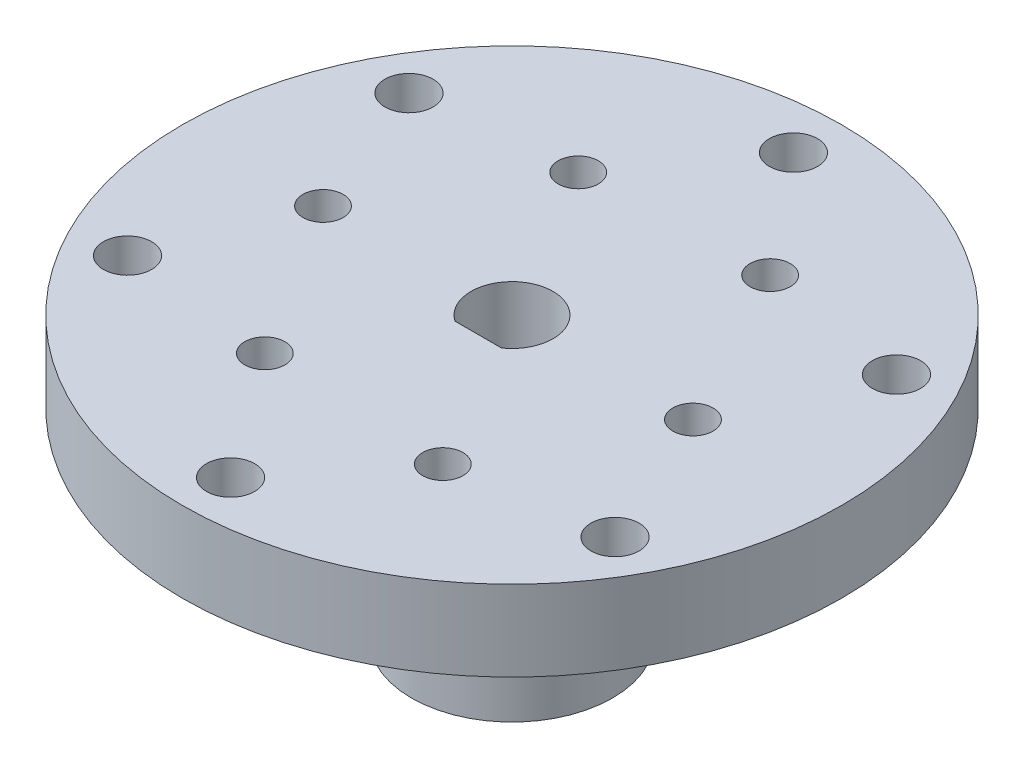
SolidWorks part; units mm, degrees
material "6061 Alloy"
ref_plane "Front Plane" through (0, 0, 0) normal (0, 0, 1) x (1, 0, 0)
ref_plane "Top Plane" through (0, 0, 0) normal (0, 1, 0) x (1, 0, 0)
ref_plane "Right Plane" through (0, 0, 0) normal (1, 0, 0) x (0, 0, -1)
sketch "Sketch1" plane through (0, 0, 0) normal (0, 1, 0) x (1, 0, 0)
  circle A0 centre (0, 0) radius 5.1
  circle A1 centre (0, 0) radius 12.5
  dimension "D1" = 10.2
  dimension "D2" = 25
extrude "Boss-Extrude1" add sketch "Sketch1" along normal blind 15
sketch "Sketch2" plane through (0, 15, 0) normal (0, 1, 0) x (1, 0, 0)
  circle A0 centre (0, 0) radius 5.1
  circle A1 centre (0, 0) radius 41
  circle A3 centre (0, 0) radius 5.1 construction
  dimension "D1" = 82
extrude "Boss-Extrude2" add sketch "Sketch2" along normal blind 20
sketch "Sketch3" plane through (0, 35, 0) normal (0, 1, 0) x (1, 0, 0)
  circle A0 centre (0, 0) radius 35 construction
  circle A1 centre (0, 35) radius 3
  circle A2 centre (30.3109, 17.5) radius 3
  circle A3 centre (30.3109, -17.5) radius 3
  circle A4 centre (0, -35) radius 3
  circle A5 centre (-30.3109, -17.5) radius 3
  circle A6 centre (-30.3109, 17.5) radius 3
  point P17 (0, 0)
  dimension "D1" = 70
  dimension "D2" = 6
  dimension "D3" = 6
extrude "Cut-Extrude1" cut sketch "Sketch3" against normal through all
sketch "Sketch4" plane through (0, 0, 0) normal (0, -1, 0) x (1, 0, 0)
  line L0 (-2.8931, 4.2) -> (2.8931, 4.2)
  circle A0 centre (0, 0) radius 5.1
  circle A1 centre (0, 0) radius 5.1 construction
  circle M3 centre (0, 0) radius 5.1
  dimension "D1" = 4.2
extrude "Boss-Extrude3" add sketch "Sketch4" against normal blind 35 contours L0 M3
sketch "Sketch5" plane through (0, 0, 4.2) normal (0, 0, -1) x (-1, 0, 0)
  line L0 (0, 35) -> (0, 0) construction
  line L1 (2.8931, 35) -> (-2.8931, 35) construction
  line L2 (2.8931, 0) -> (-2.8931, 0) construction
  circle A0 centre (0, 9) radius 1.5
  dimension "D1" = 3
  dimension "D2" = 9
extrude "Cut-Extrude2" cut sketch "Sketch5" against normal through all and the other way through all
sketch "Sketch6" plane through (0, 15, 0) normal (0, -1, 0) x (1, 0, 0)
  circle A0 centre (0, 0) radius 12.5
  circle A1 centre (0, 0) radius 41
  circle A2 centre (0, 0) radius 41 construction
  circle A3 centre (0, 0) radius 12.5 construction
extrude "Cut-Extrude3" cut sketch "Sketch6" against normal blind 10
sketch "Sketch7" plane through (0, 35, 0) normal (0, 1, 0) x (1, 0, 0)
  circle A0 centre (-2.8931, -4.2) radius 0.7109
  circle A1 centre (2.8931, -4.2) radius 0.682
sketch "Sketch8" plane through (0, 0, 0) normal (0, -1, 0) x (1, 0, 0)
  circle A0 centre (0, 0) radius 22.5 construction
  circle A1 centre (22.5, 0) radius 2.5
  circle A2 centre (0, 0) radius 23.5 construction
  circle A3 centre (-23.5, 0) radius 2.5
  circle A4 centre (-11.25, -19.4856) radius 2.5
  circle A5 centre (-11.25, 19.4856) radius 2.5
  circle A6 centre (11.75, 20.3516) radius 2.5
  circle A7 centre (11.75, -20.3516) radius 2.5
  point P14 (0, 0)
  point P19 (0, 0)
  dimension "D1" = 45
  dimension "D2" = 1
  dimension "D3" = 5
  dimension "D4" = 5
  dimension "D5" = 3
  dimension "D6" = 3
extrude "Cut-Extrude4" cut sketch "Sketch8" against normal through all
